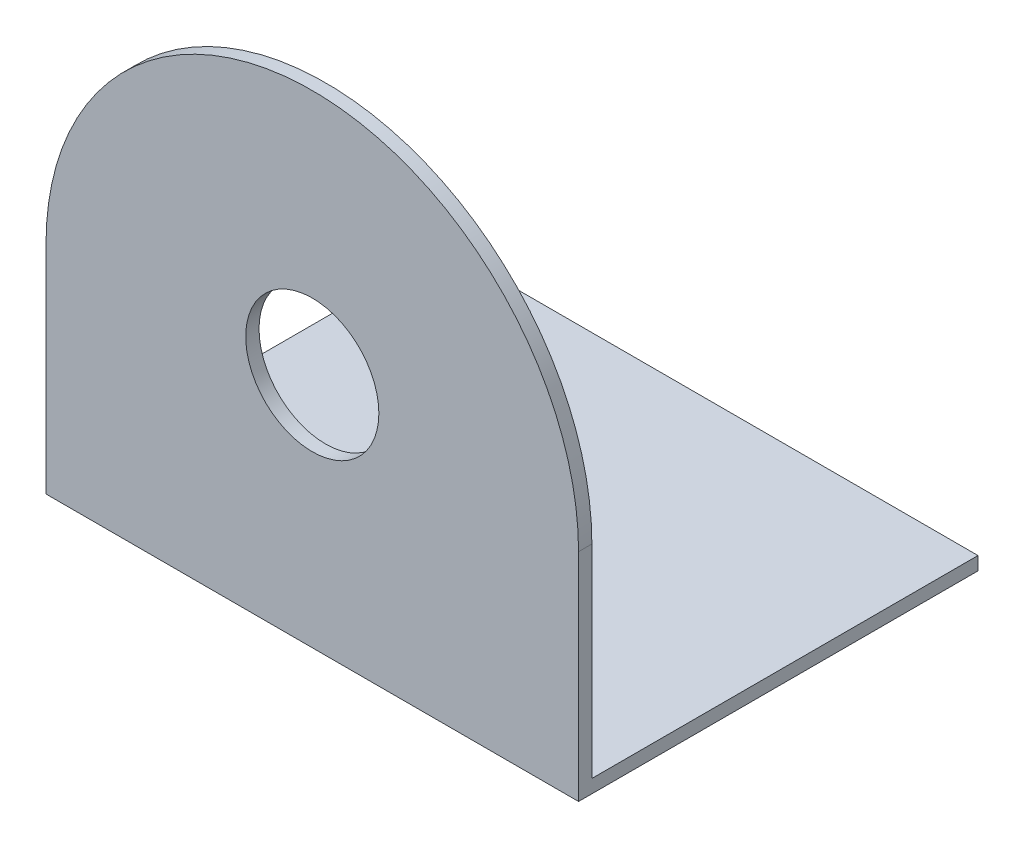
SolidWorks part; units mm, degrees
ref_plane "Front Plane" through (0, 0, 0) normal (0, 0, 1) x (1, 0, 0)
ref_plane "Top Plane" through (0, 0, 0) normal (0, 1, 0) x (1, 0, 0)
ref_plane "Right Plane" through (0, 0, 0) normal (1, 0, 0) x (0, 0, -1)
sketch "Sketch3" plane through (0, 0, 0) normal (0, 0, 1) x (1, 0, 0)
  line L0 (-20, 0) -> (-20, -15.25)
  line L1 (0, 0) -> (0, -5.8781) construction
  line L2 (20, 0) -> (20, -15.25)
  line L3 (-20, -15.25) -> (20, -15.25)
  arc A0 (-20, 0) -> (20, 0) centre (0, 0) cw
  dimension "D2" = 20
  dimension "D1" = 40
  dimension "D3" = 40
  dimension "D4" = 20
  dimension "D5" = 15.25
extrude "Boss-Extrude1" add sketch "Sketch3" along normal blind 1
sketch "Sketch4" plane through (0, 0, 1) normal (0, 0, 1) x (1, 0, 0)
  line L1 (20, -15.25) -> (-20, -15.25)
  line L2 (20, -15.25) -> (20, -16.25)
  line L3 (20, -16.25) -> (-20, -16.25)
  line L4 (-20, -15.25) -> (-20, -16.25)
  dimension "D1" = 1
extrude "Boss-Extrude2" add sketch "Sketch4" against normal blind 30
sketch "Sketch5" plane through (0, 0, 1) normal (0, 0, 1) x (1, 0, 0)
  line L1 (-20, -16.25) -> (20, -16.25) construction
  circle A1 centre (0, 1.5) radius 5
  dimension "D1" = 10
  dimension "D2" = 17.75
extrude "Cut-Extrude1" cut sketch "Sketch5" against normal blind 47
